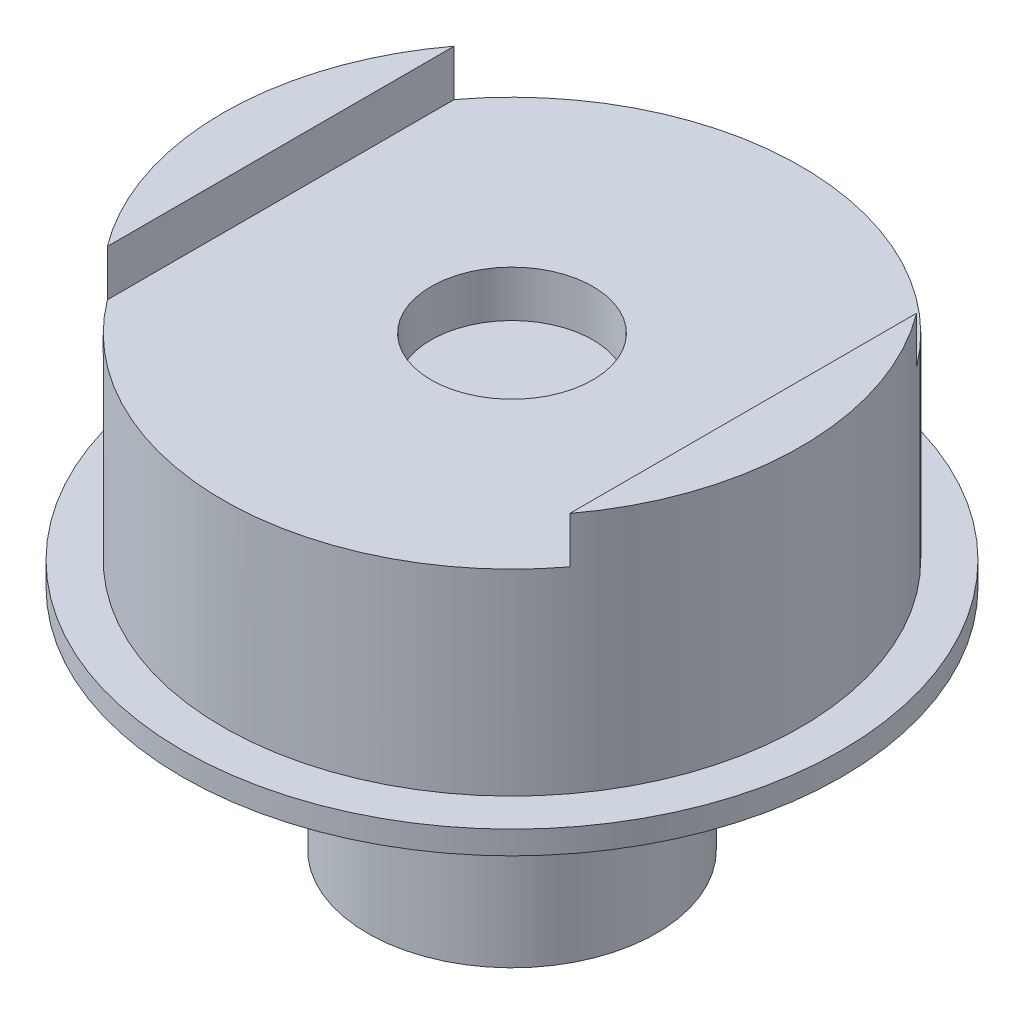
SolidWorks part; units mm, degrees
ref_plane "前基準面" through (0, 0, 0) normal (0, 0, 1) x (1, 0, 0)
ref_plane "上基準面" through (0, 0, 0) normal (0, 1, 0) x (1, 0, 0)
ref_plane "右基準面" through (0, 0, 0) normal (1, 0, 0) x (0, 0, -1)
sketch "草圖1" plane through (0, 0, 0) normal (0, 0, 1) x (1, 0, 0)
  line L0 (0, 41.9211) -> (0, 2.3) construction
  line L3 (0, 21) -> (25, 21)
  line L4 (25, 21) -> (25, 0)
  line L5 (25, 0) -> (28.5, 0)
  line L6 (28.5, 0) -> (28.5, -2)
  line L7 (28.5, -2) -> (12.5, -2)
  line L8 (12.5, -2) -> (12.5, -21.7)
  line L9 (12.5, -21.7) -> (8, -21.7)
  line L10 (0, 21) -> (0, 2.3)
  line L13 (0, 2.3) -> (8, 2.3)
  line L14 (8, 2.3) -> (8, -21.7)
  point P1 (0, 2.3)
  point P3 (0, 0)
  point P5 (28.5, -1)
  dimension "D1" = 19.7
  dimension "D2" = 2
  dimension "D3" = 21
  dimension "D4" = 16
  dimension "D5" = 24
  dimension "D6" = 57
  dimension "D7" = 25
  dimension "D8" = 50
revolve "旋轉1" add sketch "草圖1" angle 360 about L0
sketch "草圖2" plane through (0, 21, 0) normal (0, 1, 0) x (1, 0, 0)
  line L1 (-20, -28.5) -> (20, -28.5)
  line L2 (-20, -28.5) -> (-20, 28.5)
  line L3 (-20, 28.5) -> (20, 28.5)
  line L4 (20, -28.5) -> (20, 28.5)
  line L5 (-20, -28.5) -> (20, 28.5) construction
  line L6 (-20, 28.5) -> (20, -28.5) construction
  circle A0 centre (0, 0) radius 28.5 construction
  point P0 (0, 0)
  dimension "D1" = 40
extrude "除料-伸長1" cut sketch "草圖2" against normal blind 4
sketch "草圖3" plane through (0, 17, 0) normal (0, 1, 0) x (1, 0, 0)
  circle A0 centre (0, 0) radius 7
  dimension "D1" = 14
extrude "除料-伸長3" cut sketch "草圖3" against normal blind 4
